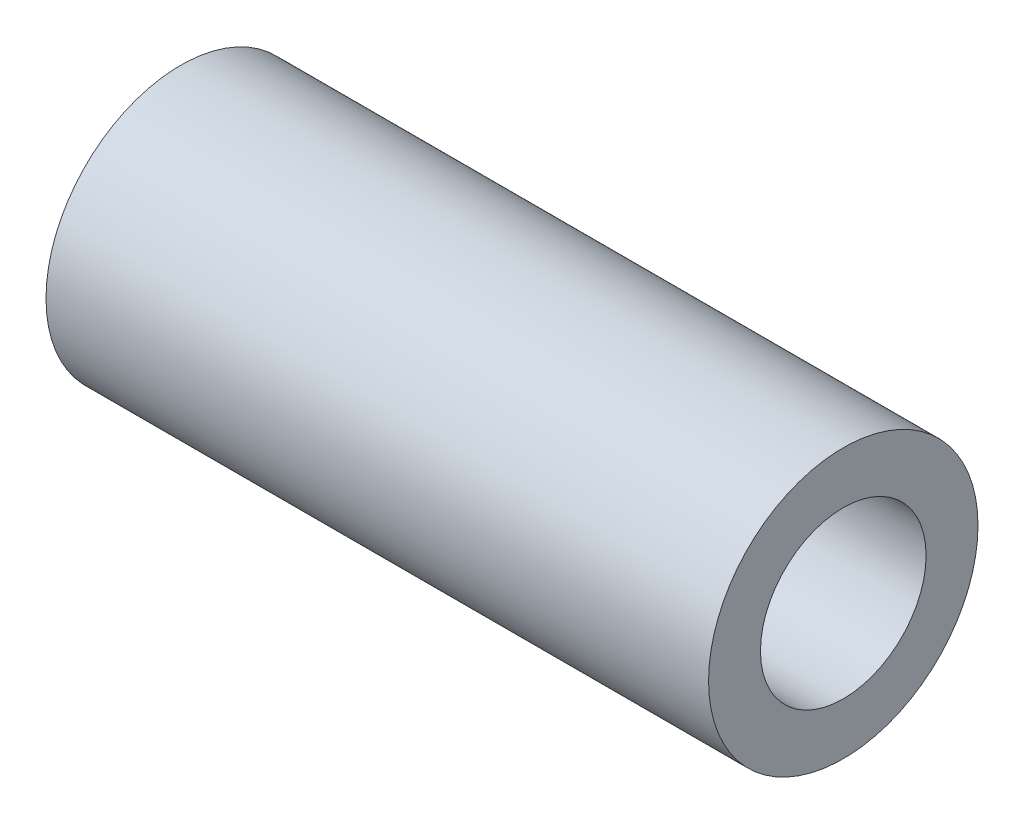
SolidWorks part; units mm, degrees
ref_plane "Front Plane" through (0, 0, 0) normal (0, 0, 1) x (1, 0, 0)
ref_plane "Top Plane" through (0, 0, 0) normal (0, 1, 0) x (1, 0, 0)
ref_plane "Right Plane" through (0, 0, 0) normal (1, 0, 0) x (0, 0, -1)
sketch "Sketch1" plane through (0, 0, 0) normal (0, 1, 0) x (1, 0, 0)
  line L0 (0, 0) -> (0, 3.8735)
  line L1 (0, 3.8735) -> (19.05, 3.8735)
  line L2 (19.05, 3.8735) -> (19.05, 2.3813)
  line L3 (19.05, 2.3813) -> (12.7, 2.3813)
  line L4 (12.7, 2.3813) -> (12.7, 0)
  line L5 (12.7, 0) -> (0, 0)
  dimension "D1" = 3.8735
  dimension "D2" = 2.3813
  dimension "D3" = 6.35
  dimension "D4" = 12.7
revolve "Revolve1" add sketch "Sketch1" angle 360 about L5
